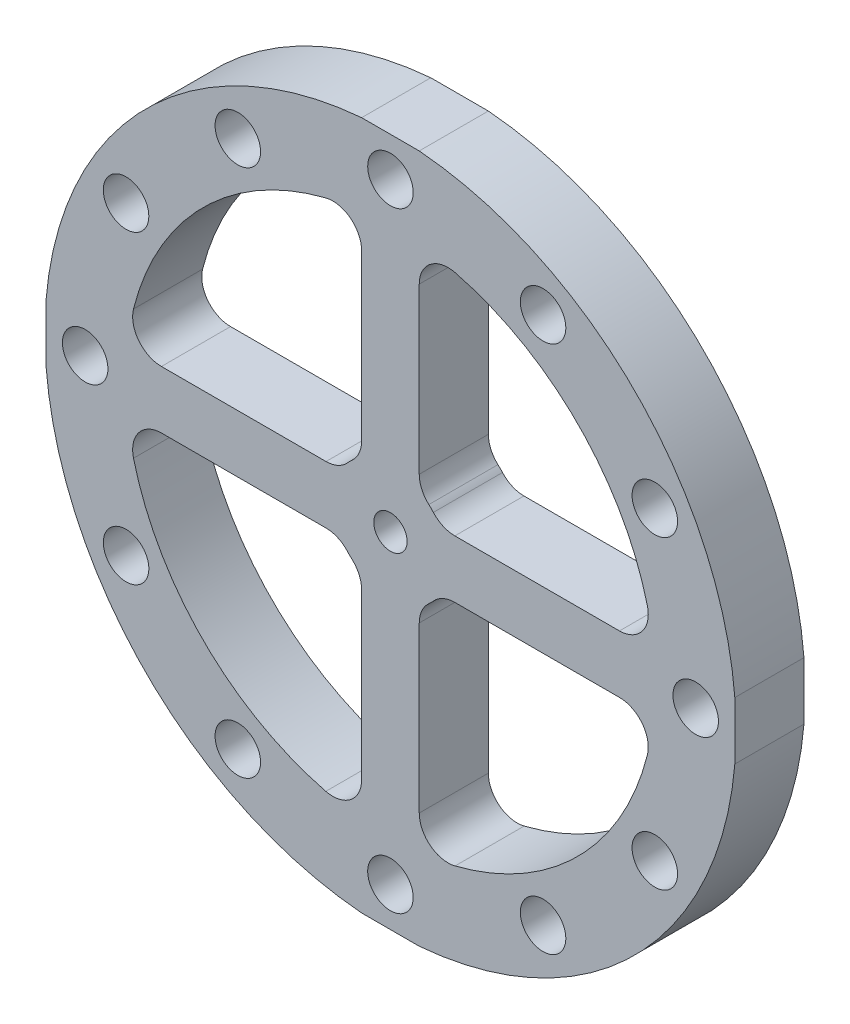
SolidWorks part; units mm, degrees
ref_plane "Ebene vorne" through (0, 0, 0) normal (0, 0, 1) x (1, 0, 0)
ref_plane "Ebene oben" through (0, 0, 0) normal (0, 1, 0) x (1, 0, 0)
ref_plane "Ebene rechts" through (0, 0, 0) normal (1, 0, 0) x (0, 0, -1)
other "Massenmittelpunkt"
sketch "Skizze1" plane through (0, 0, 0) normal (0, 0, 1) x (1, 0, 0)
  line L0 (-60, 0) -> (60, 0) construction
  line L1 (0, 60) -> (0, -60) construction
  line L3 (-59.7913, -5) -> (59.7913, -5)
  line L4 (-59.7913, -5) -> (-59.7913, 5)
  line L5 (-59.7913, 5) -> (59.7913, 5)
  line L6 (59.7913, -5) -> (59.7913, 5)
  line L7 (-59.7913, -5) -> (59.7913, 5) construction
  line L8 (-59.7913, 5) -> (59.7913, -5) construction
  line L9 (-5, -59.7913) -> (5, -59.7913)
  line L10 (-5, -59.7913) -> (-5, 59.7913)
  line L11 (-5, 59.7913) -> (5, 59.7913)
  line L12 (5, -59.7913) -> (5, 59.7913)
  line L13 (-5, -59.7913) -> (5, 59.7913) construction
  line L14 (-5, 59.7913) -> (5, -59.7913) construction
  circle A2 centre (0, 0) radius 60
  circle A3 centre (0, 0) radius 2.9
  circle A4 centre (0, 0) radius 10
  circle A5 centre (0, 0) radius 46
  dimension "D1" = 5.8
  dimension "D2" = 120
  dimension "D3" = 20
  dimension "D4" = 14
  dimension "D5" = 10
  dimension "D6" = 10
extrude "Aufsatz-Linear austragen3" add sketch "Skizze1" along normal blind 12 contours A5 L5 L4 L3 | L5 A5 L3 A4 | L3 L12 L5 L10 A3 | L5 A4 L3 L10 | L10 A4 L5 | L12 A4 L10 L5 | L5 A4 L12 | L3 A4 L5 L12 | L3 A5 L5 A4 | A5 L3 L6 L5 | A5 L5 A2 L12 | A5 L12 L11 L10 | A5 L10 A2 L5 | L12 A5 L10 A4 | L3 A4 L10 | L10 A4 L12 L3 | L12 A4 L3 | L10 A5 L12 A4 | A5 L3 A2 L10 | A5 L10 L9 L12 | A5 L12 A2 L3
sketch "Skizze2" plane through (0, 0, 12) normal (0, 0, 1) x (1, 0, 0)
  circle A0 centre (0, 0) radius 53
  circle A1 centre (0, -53) radius 3.95
  dimension "D1" = 106
  dimension "D2" = 7.9
extrude "Schnitt-Linear austragen1" cut sketch "Skizze2" against normal blind 12 contours A0 A1 | A0 A1
pattern_circular "Kreismuster1" count 12 over 360 about axis through (0, 0, 0) along (0, 0, 1) of "Schnitt-Linear austragen1"
fillet "Verrundung1" radius 5 16 edges at (5, 45.7275, 6) (5, -45.7275, 6) (-45.7275, -5, 6) (45.7275, -5, 6) (-45.7275, 5, 6) (45.7275, 5, 6) (-5, -45.7275, 6) (-5, 45.7275, 6) (-5, -8.6603, 6) (-5, 8.6603, 6) (-8.6603, 5, 6) (8.6603, 5, 6) (5, 8.6603, 6) (5, -8.6603, 6) (-8.6603, -5, 6) (8.6603, -5, 6)
